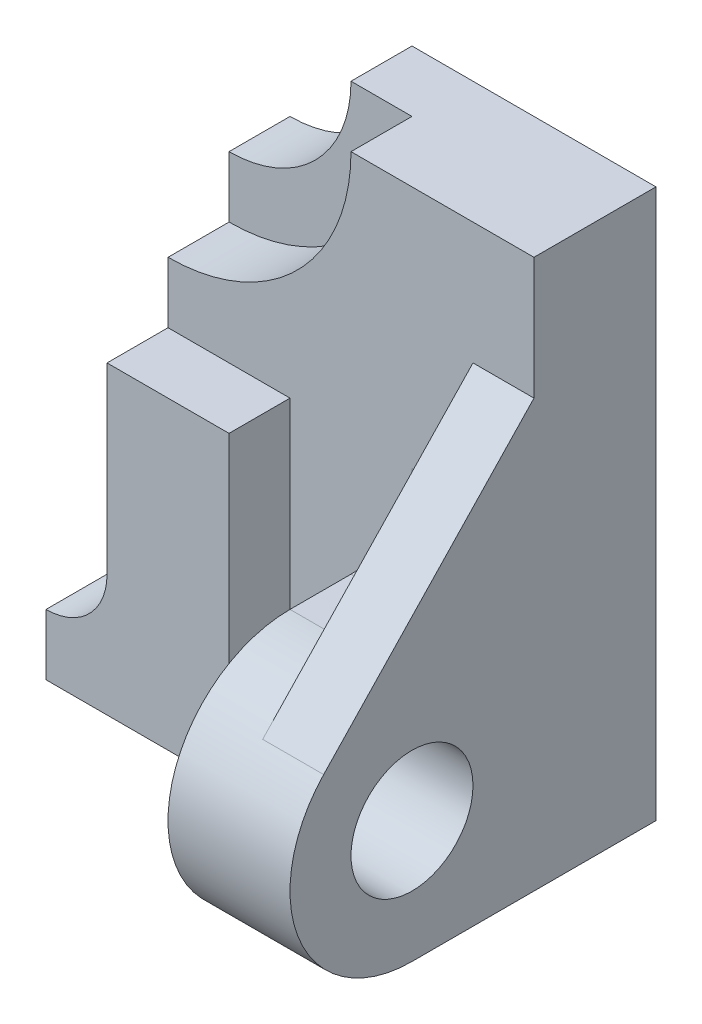
SolidWorks part; units mm, degrees
ref_plane "Front Plane" through (0, 0, 0) normal (0, 0, 1) x (1, 0, 0)
ref_plane "Top Plane" through (0, 0, 0) normal (0, 1, 0) x (1, 0, 0)
ref_plane "Right Plane" through (0, 0, 0) normal (1, 0, 0) x (0, 0, -1)
sketch "Sketch1" plane through (0, 0, 0) normal (0, 0, 1) x (1, 0, 0)
  line L1 (3, -4.5) -> (-3, -4.5)
  line L2 (3, -4.5) -> (3, 4.5)
  line L3 (3, 4.5) -> (-3, 4.5)
  line L4 (-3, -4.5) -> (-3, 4.5)
  line L5 (3, -4.5) -> (-3, 4.5) construction
  line L6 (3, 4.5) -> (-3, -4.5) construction
  point P0 (0, 0)
  dimension "D1" = 6
  dimension "D2" = 9
extrude "Boss-Extrude1" add sketch "Sketch1" along normal blind 2
sketch "Sketch2" plane through (0, 0, 2) normal (0, 0, 1) x (1, 0, 0)
  line L0 (3, 4.5) -> (-3, 4.5) construction
  line L1 (-3, 4.5) -> (-3, -4.5) construction
  line L2 (-1, 4.5) -> (-3, 4.5)
  line L3 (-3, 4.5) -> (-3, 2.5)
  arc A0 (-1, 4.5) -> (-3, 2.5) centre (-3, 4.5) cw
  dimension "D1" = 2
extrude "Cut-Extrude1" cut sketch "Sketch2" against normal through all
sketch "Sketch3" plane through (0, 0, 2) normal (0, 0, 1) x (1, 0, 0)
  line L0 (3, 4.5) -> (-1, 4.5) construction
  line L1 (-3, 2.5) -> (-3, -4.5) construction
  line L2 (0, 4.5) -> (-3, 4.5)
  line L3 (-3, 4.5) -> (-3, 1.5)
  arc A0 (0, 4.5) -> (-3, 1.5) centre (-3, 4.5) cw
  dimension "D1" = 3
extrude "Cut-Extrude2" cut sketch "Sketch3" against normal blind 1
sketch "Sketch4" plane through (0, 0, 2) normal (0, 0, 1) x (1, 0, 0)
  line L0 (-3, -4.5) -> (-3, 0.5)
  line L1 (-3, 1.5) -> (-3, -4.5) construction
  line L2 (-3, 0.5) -> (-1, 0.5)
  line L3 (-1, 0.5) -> (-1, -4.5)
  line L4 (-3, -4.5) -> (3, -4.5) construction
  line L5 (-1, -4.5) -> (-3, -4.5)
  dimension "D1" = 2
  dimension "D2" = 5
extrude "Boss-Extrude2" add sketch "Sketch4" along normal blind 1
sketch "Sketch5" plane through (0, 0, 3) normal (0, 0, 1) x (1, 0, 0)
  line L0 (-3, -4.5) -> (-4, -4.5)
  line L1 (-4, -4.5) -> (-4, -3.5)
  line L2 (-3, 0.5) -> (-3, -4.5) construction
  line L3 (-3, -2.5) -> (-3, -4.5)
  arc A0 (-4, -3.5) -> (-3, -2.5) centre (-4, -2.5) ccw
  dimension "D1" = 1
  dimension "D2" = 1
  dimension "D3" = 2
extrude "Boss-Extrude3" add sketch "Sketch5" against normal blind 3
sketch "Sketch7" plane through (3, 0, 0) normal (1, 0, 0) x (0, 0, -1)
  line L0 (-2, -4.5) -> (-4, -4.5)
  line L1 (-4, -0.5) -> (-3, -0.5)
  line L2 (-3, -4.5) -> (-3, 0.5) construction
  arc A0 (-4, -4.5) -> (-4, -0.5) centre (-4, -2.5) cw
  arc A1 (-3, -0.5) -> (-2, 0.5) centre (-3, 0.5) ccw
  circle A2 centre (-4, -2.5) radius 1
  point P3 (-4, -2.5)
  line M3 (-2, 4.5) -> (-2, -4.5)
  dimension "D4" = 2
  dimension "D1" = 2
  dimension "D2" = 2
  dimension "D3" = 1
extrude "Boss-Extrude4" add sketch "Sketch7" against normal blind 2 contours A1 L1 A0 L0 A2 M3
sketch "Sketch8" plane through (3, 0, 0) normal (1, 0, 0) x (0, 0, -1)
  line L0 (-2, 2.5) -> (-5.4483, -1.1207)
  line L1 (-2, 0.5) -> (-2, 4.5) construction
  line L2 (-2, 2.5) -> (-2, 0.5)
  line L3 (-3, -0.5) -> (-4, -0.5)
  arc A0 (-4, -0.5) -> (-4, -4.5) centre (-4, -2.5) ccw construction
  arc A1 (-2, 0.5) -> (-3, -0.5) centre (-3, 0.5) cw
  arc A2 (-5.4483, -1.1207) -> (-4, -0.5) centre (-4, -2.5) cw
  dimension "D1" = 2
extrude "Boss-Extrude5" add sketch "Sketch8" against normal blind 1
